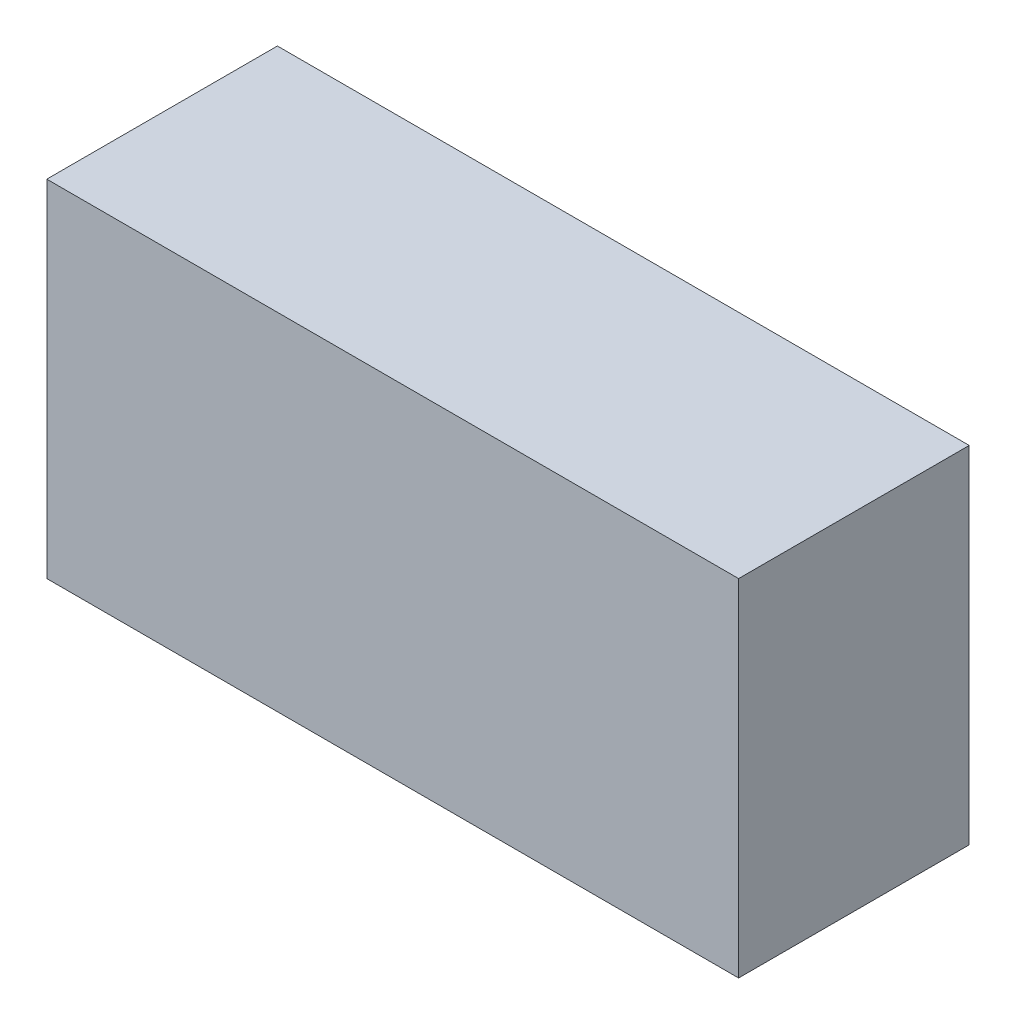
SolidWorks part; units mm, degrees
ref_plane "Płaszczyzna przednia" through (0, 0, 0) normal (0, 0, 1) x (1, 0, 0)
ref_plane "Płaszczyzna górna" through (0, 0, 0) normal (0, 1, 0) x (1, 0, 0)
ref_plane "Płaszczyzna prawa" through (0, 0, 0) normal (1, 0, 0) x (0, 0, -1)
sketch "Szkic2" plane through (0, 0, 0) normal (0, 0, 1) x (1, 0, 0)
  line L1 (-27.7612, 64.2537) -> (32.2388, 64.2537)
  line L2 (-27.7612, 64.2537) -> (-27.7612, 34.2537)
  line L3 (-27.7612, 34.2537) -> (32.2388, 34.2537)
  line L4 (32.2388, 64.2537) -> (32.2388, 34.2537)
  dimension "D1" = 60
  dimension "D2" = 30
extrude "Dodanie-wyciągnięcie1" add sketch "Szkic2" along normal blind 20 contours L1 L4 L3 L2
sketch "Szkic3" plane through (-27.7612, 0, 0) normal (-1, 0, 0) x (0, 0, 1)
  line L1 (-1.1571, 55.2717) -> (21.5774, 55.2717)
  line L2 (-1.1571, 55.2717) -> (-1.1571, 40.7522)
  line L3 (-1.1571, 40.7522) -> (21.5774, 40.7522)
  line L4 (21.5774, 55.2717) -> (21.5774, 40.7522)
  dimension "D1" = 22.7345
  dimension "D2" = 14.5195
